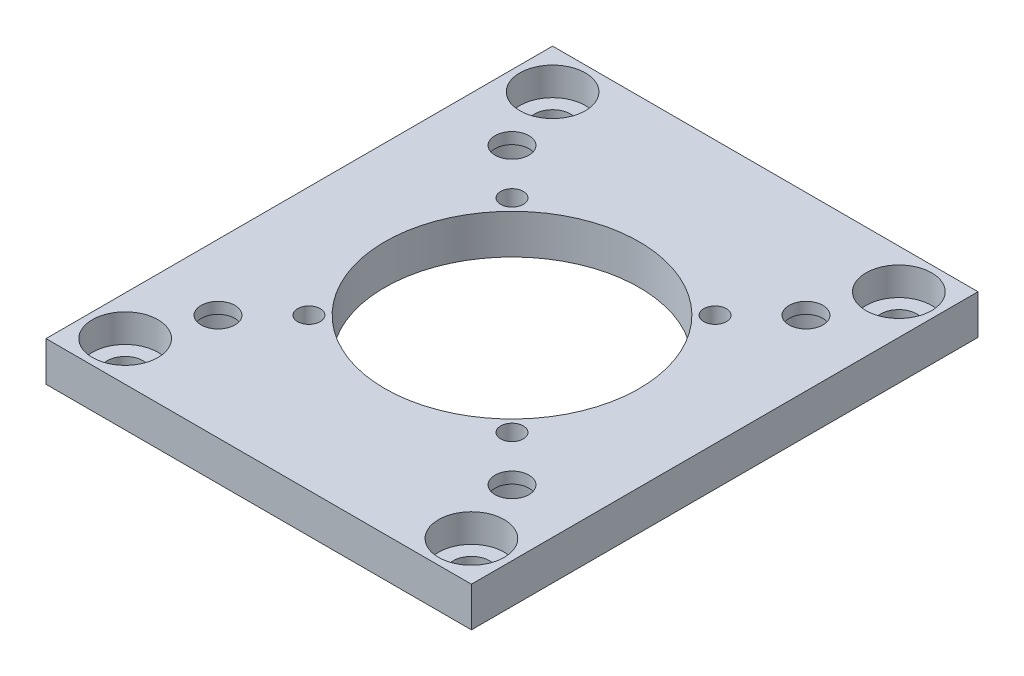
SolidWorks part; units mm, degrees
ref_plane "Front Plane" through (0, 0, 0) normal (0, 0, 1) x (1, 0, 0)
ref_plane "Top Plane" through (0, 0, 0) normal (0, 1, 0) x (1, 0, 0)
ref_plane "Right Plane" through (0, 0, 0) normal (1, 0, 0) x (0, 0, -1)
sketch "Sketch2" plane through (0, 0, 0) normal (0, 1, 0) x (1, 0, 0)
  line L0 (0, -13) -> (0, 13) construction
  line L1 (-13, 13) -> (13, 13) construction
  line L2 (-13, 13) -> (-13, -13) construction
  line L3 (-13, -13) -> (13, -13) construction
  line L4 (13, 13) -> (13, -13) construction
  line L5 (-13, 0) -> (13, 0) construction
  line L7 (-18.8109, -22.4) -> (18.8109, -22.4)
  line L9 (-18.8109, 22.4) -> (18.8109, 22.4)
  line L10 (18.8109, -22.4) -> (18.8109, 22.4)
  line L11 (-18.8109, -22.4) -> (18.8109, 22.4) construction
  line L12 (-18.8109, 22.4) -> (18.8109, -22.4) construction
  line L15 (-18.8109, 22.4) -> (-18.8109, -22.4)
  circle A0 centre (0, 0) radius 11.25
  circle A1 centre (-13, 13) radius 1.5
  circle A2 centre (13, 13) radius 1.5
  circle A3 centre (13, -13) radius 1.5
  circle A4 centre (-13, -13) radius 1.5
  circle A5 centre (8.98, 8.98) radius 1
  circle A6 centre (-8.98, 8.98) radius 1
  circle A7 centre (8.98, -8.98) radius 1
  circle A8 centre (-8.98, -8.98) radius 1
  circle A9 centre (-15.31, 18.9) radius 1.6
  circle A10 centre (15.31, 18.9) radius 1.6
  circle A11 centre (15.31, -18.9) radius 1.6
  circle A12 centre (-15.31, -18.9) radius 1.6
  point P15 (0, 0)
  dimension "D1" = 22.5
  dimension "D2" = 3
  dimension "D6" = 2
  dimension "D9" = 3.5
  dimension "D10" = 3.2
  dimension "D11" = 30.62
  dimension "D7" = 17.96
  dimension "D3" = 26
  dimension "D4" = 37.6219
  dimension "D5" = 44.8
  dimension "D8" = 8.98
extrude "Boss-Extrude1" add sketch "Sketch2" along normal blind 3.5
sketch "Sketch4" plane through (0, 0, 0) normal (0, -1, 0) x (1, 0, 0)
  line L0 (-11.25, 0) -> (11.25, 0) construction
  line L1 (0, -11.25) -> (0, 11.25) construction
  circle A0 centre (-13, -13) radius 2.9
  circle A1 centre (0, 0) radius 11.25 construction
  circle A2 centre (13, -13) radius 2.9
  circle A3 centre (13, 13) radius 2.9
  circle A4 centre (-13, 13) radius 2.9
  dimension "D1" = 5.8
extrude "Cut-Extrude1" cut sketch "Sketch4" against normal blind 2.5
sketch "Sketch6" plane through (0, 3.5, 0) normal (0, 1, 0) x (1, 0, 0)
  line L0 (0, -22.4) -> (0, 22.4) construction
  line L1 (18.8109, 22.4) -> (-18.8109, 22.4) construction
  line L3 (18.8109, 0) -> (-18.8109, 0) construction
  line L6 (18.8109, -22.4) -> (18.8109, 22.4) construction
  line L8 (-18.8109, -22.4) -> (18.8109, -22.4) construction
  line L9 (-18.8109, 22.4) -> (-18.8109, -22.4) construction
  circle A0 centre (-15.31, 18.9) radius 2.9
  circle A1 centre (15.31, -18.9) radius 1.6 construction
  circle A2 centre (15.31, -18.9) radius 2.9
  circle A3 centre (15.31, 18.9) radius 2.9
  circle A4 centre (-15.31, -18.9) radius 2.9
  circle A5 centre (-15.31, -18.9) radius 1.6 construction
  circle A6 centre (-15.31, -18.9) radius 1.6
  circle A9 centre (15.31, 18.9) radius 1.5 construction
  dimension "D1" = 5.8
  dimension "D2" = 5.8
  dimension "D3" = 5.8
extrude "Cut-Extrude2" cut sketch "Sketch6" against normal blind 2.5
